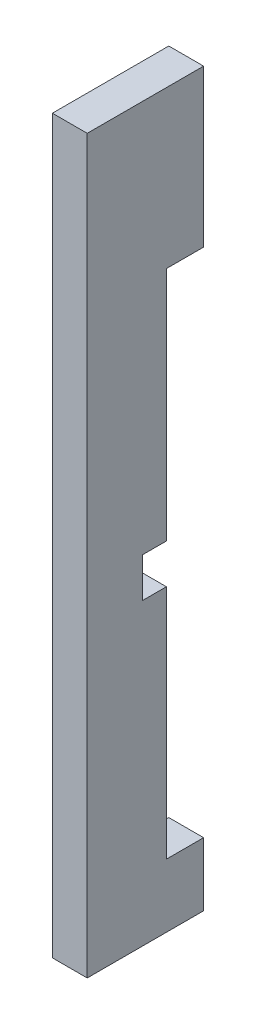
SolidWorks part; units mm, degrees
material "Chêne"
ref_plane "Plan de face" through (0, 0, 0) normal (0, 0, 1) x (1, 0, 0)
ref_plane "Plan de dessus" through (0, 0, 0) normal (0, 1, 0) x (1, 0, 0)
ref_plane "Plan de droite" through (0, 0, 0) normal (1, 0, 0) x (0, 0, -1)
sketch "Esquisse1" plane through (0, 0, 0) normal (0, 0, 1) x (1, 0, 0)
  line L1 (140, 261) -> (118, 261)
  line L2 (140, 261) -> (140, -201)
  line L3 (140, -201) -> (118, -201)
  line L4 (118, 261) -> (118, -201)
  dimension "D1" = 22
  dimension "D2" = 462
  dimension "D3" = 261
  dimension "D4" = 140
extrude "Boss.-Extru.1" add sketch "Esquisse1" along normal blind 73.5
sketch "Esquisse2" plane through (118, 0, 0) normal (-1, 0, 0) x (0, 0, 1)
  line L0 (73.5, 261) -> (0, 261) construction
  line L4 (0, 13) -> (38.5, 13)
  line L5 (0, -12) -> (0, 13)
  line L6 (38.5, -12) -> (0, -12)
  line L7 (38.5, 13) -> (38.5, -12)
  line L11 (0, 261) -> (0, -201) construction
  dimension "D1" = 38.5
  dimension "D2" = 25
  dimension "D3" = 248
extrude "Enlèv. mat.-Extru.1" cut sketch "Esquisse2" against normal blind 35
sketch "Esquisse3" plane through (140, 0, 0) normal (1, 0, 0) x (0, 0, -1)
  line L0 (0, 13) -> (0, 261) construction
  line L1 (0, 162) -> (-23.5, 162)
  line L2 (0, 162) -> (0, -161)
  line L3 (0, -161) -> (-23.5, -161)
  line L4 (-23.5, 162) -> (-23.5, -161)
  line L6 (-73.5, 261) -> (0, 261) construction
  line L7 (-73.5, -201) -> (0, -201) construction
  dimension "D1" = 99
  dimension "D2" = 40
  dimension "D3" = 23.5
extrude "Enlèv. mat.-Extru.2" cut sketch "Esquisse3" against normal blind 35
